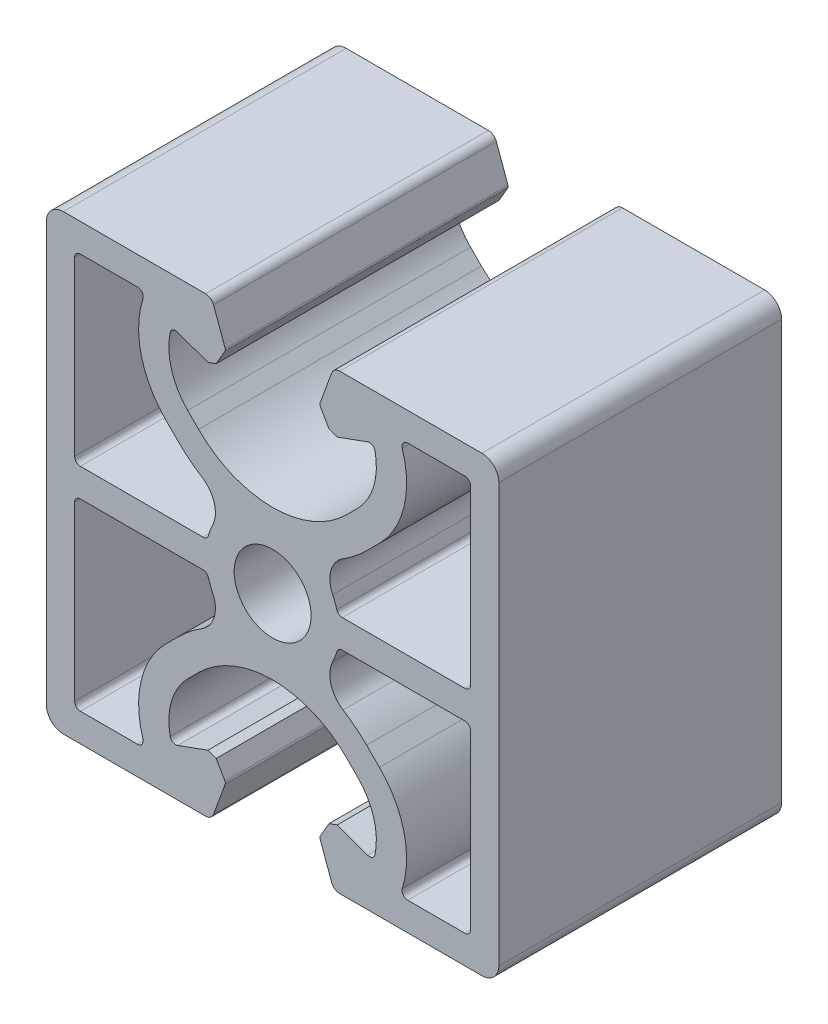
SolidWorks part; units mm, degrees
material "6005-T5"
ref_plane "Front" through (0, 0, 0) normal (0, 0, 1) x (1, 0, 0)
ref_plane "Top" through (0, 0, 0) normal (0, 1, 0) x (1, 0, 0)
ref_plane "Right" through (0, 0, 0) normal (1, 0, 0) x (0, 0, -1)
sketch "Sk Main Extrusion" plane through (0, 0, 0) normal (0, 0, 1) x (1, 0, 0)
  line L46 (-8.3085, 7.4415) -> (-9.4443, 8.5773)
  line L47 (-11.9407, 17.5) -> (-17, 17.5)
  line L48 (-17.5, 17) -> (-17.5, 1.75)
  line L49 (-17, 1.25) -> (-6.1561, 1.25)
  line L50 (-17.5, -1.75) -> (-17.5, -17)
  line L51 (-17, -17.5) -> (-11.9407, -17.5)
  line L52 (-9.4443, -8.5773) -> (-8.3085, -7.4415)
  line L53 (-6.1561, -1.25) -> (-17, -1.25)
  line L54 (9.4443, 8.5773) -> (8.3085, 7.4415)
  line L55 (6.1561, 1.25) -> (17, 1.25)
  line L56 (17.5, 1.75) -> (17.5, 17)
  line L57 (17, 17.5) -> (11.9407, 17.5)
  line L58 (-4.1901, 16.6712) -> (-5.2221, 19.5065)
  line L59 (-5.9268, 20) -> (-18.5, 20)
  line L60 (-18.5, -20) -> (-5.9268, -20)
  line L61 (-5.2221, -19.5065) -> (-4.1901, -16.6712)
  line L62 (-4.2085, -16.4607) -> (-4.9876, -15.1113)
  line L63 (-4.9876, -15.1113) -> (-5.7185, -14.8453)
  line L64 (-5.7185, -14.8453) -> (-8.3962, -15.8198)
  line L65 (-7.5042, -10.2727) -> (-6.5407, -9.3093)
  line L66 (6.5407, -9.3093) -> (7.5042, -10.2727)
  line L67 (8.3962, -15.8198) -> (5.7185, -14.8453)
  line L68 (5.7185, -14.8453) -> (4.9876, -15.1113)
  line L69 (4.9876, -15.1113) -> (4.2085, -16.4607)
  line L70 (20, -18.5) -> (20, 18.5)
  line L71 (-20, 18.5) -> (-20, -18.5)
  line L72 (8.3085, -7.4415) -> (9.4443, -8.5773)
  line L73 (11.9407, -17.5) -> (17, -17.5)
  line L74 (17.5, -17) -> (17.5, -1.75)
  line L75 (17, -1.25) -> (6.1561, -1.25)
  line L76 (4.1901, -16.6712) -> (5.2221, -19.5065)
  line L77 (5.9268, -20) -> (18.5, -20)
  line L78 (18.5, 20) -> (5.9268, 20)
  line L79 (5.2221, 19.5065) -> (4.1901, 16.6712)
  line L80 (4.2085, 16.4607) -> (4.9876, 15.1113)
  line L81 (4.9876, 15.1113) -> (5.7185, 14.8453)
  line L82 (5.7185, 14.8453) -> (8.3962, 15.8198)
  line L83 (7.5042, 10.2727) -> (6.5407, 9.3093)
  line L84 (-6.5407, 9.3093) -> (-7.5042, 10.2727)
  line L85 (-8.3962, 15.8198) -> (-5.7185, 14.8453)
  line L86 (-5.7185, 14.8453) -> (-4.9876, 15.1113)
  line L87 (-4.9876, 15.1113) -> (-4.2085, 16.4607)
  circle A55 centre (0, 0) radius 3.4
  arc A56 (-6.1561, 1.25) -> (-5.6751, 1.6133) centre (-6.1561, 1.75) ccw
  arc A57 (-5.3076, 2.5767) -> (-5.6751, 1.6133) centre (0, 0) ccw
  arc A58 (-5.3076, 2.5767) -> (-6.2308, 5.7881) centre (-7.5566, 3.6686) ccw
  arc A59 (-8.3085, 7.4415) -> (-6.2308, 5.7881) centre (0, 15.75) ccw
  arc A60 (-11.464, 16.8492) -> (-9.4443, 8.5773) centre (-3.646, 14.3755) ccw
  arc A61 (-11.464, 16.8492) -> (-11.9407, 17.5) centre (-11.9407, 17) ccw
  arc A62 (-17, 17.5) -> (-17.5, 17) centre (-17, 17) ccw
  arc A63 (-17.5, 1.75) -> (-17, 1.25) centre (-17, 1.75) ccw
  arc A64 (-5.2221, 19.5065) -> (-5.9268, 20) centre (-5.9268, 19.25) ccw
  arc A65 (-5.9268, -20) -> (-5.2221, -19.5065) centre (-5.9268, -19.25) ccw
  arc A66 (-4.1901, -16.6712) -> (-4.2085, -16.4607) centre (-4.425, -16.5857) ccw
  arc A67 (-9.057, -15.4507) -> (-8.3962, -15.8198) centre (-8.5672, -15.35) ccw
  arc A68 (-7.5042, -10.2727) -> (-9.057, -15.4507) centre (-3.4737, -14.3032) ccw
  arc A69 (6.5407, -9.3093) -> (-6.5407, -9.3093) centre (0, -15.85) ccw
  arc A70 (9.057, -15.4507) -> (7.5042, -10.2727) centre (3.4737, -14.3032) ccw
  arc A71 (8.3962, -15.8198) -> (9.057, -15.4507) centre (8.5672, -15.35) ccw
  arc A72 (4.2085, -16.4607) -> (4.1901, -16.6712) centre (4.425, -16.5857) ccw
  arc A73 (18.5, -20) -> (20, -18.5) centre (18.5, -18.5) ccw
  arc A74 (20, 18.5) -> (18.5, 20) centre (18.5, 18.5) ccw
  arc A75 (-18.5, 20) -> (-20, 18.5) centre (-18.5, 18.5) ccw
  arc A76 (-20, -18.5) -> (-18.5, -20) centre (-18.5, -18.5) ccw
  arc A77 (-17, -1.25) -> (-17.5, -1.75) centre (-17, -1.75) ccw
  arc A78 (-17.5, -17) -> (-17, -17.5) centre (-17, -17) ccw
  arc A79 (-11.9407, -17.5) -> (-11.464, -16.8492) centre (-11.9407, -17) ccw
  arc A80 (-9.4443, -8.5773) -> (-11.464, -16.8492) centre (-3.646, -14.3755) ccw
  arc A81 (-6.2308, -5.7881) -> (-8.3085, -7.4415) centre (0, -15.75) ccw
  arc A82 (-6.2308, -5.7881) -> (-5.3076, -2.5767) centre (-7.5566, -3.6686) ccw
  arc A83 (-5.6751, -1.6133) -> (-5.3076, -2.5767) centre (0, 0) ccw
  arc A84 (-5.6751, -1.6133) -> (-6.1561, -1.25) centre (-6.1561, -1.75) ccw
  arc A85 (11.9407, 17.5) -> (11.464, 16.8492) centre (11.9407, 17) ccw
  arc A86 (9.4443, 8.5773) -> (11.464, 16.8492) centre (3.646, 14.3755) ccw
  arc A87 (6.2308, 5.7881) -> (8.3085, 7.4415) centre (0, 15.75) ccw
  arc A88 (6.2308, 5.7881) -> (5.3076, 2.5767) centre (7.5566, 3.6686) ccw
  arc A89 (5.6751, 1.6133) -> (5.3076, 2.5767) centre (0, 0) ccw
  arc A90 (5.6751, 1.6133) -> (6.1561, 1.25) centre (6.1561, 1.75) ccw
  arc A91 (17, 1.25) -> (17.5, 1.75) centre (17, 1.75) ccw
  arc A92 (17.5, 17) -> (17, 17.5) centre (17, 17) ccw
  arc A93 (6.1561, -1.25) -> (5.6751, -1.6133) centre (6.1561, -1.75) ccw
  arc A94 (5.3076, -2.5767) -> (5.6751, -1.6133) centre (0, 0) ccw
  arc A95 (5.3076, -2.5767) -> (6.2308, -5.7881) centre (7.5566, -3.6686) ccw
  arc A96 (8.3085, -7.4415) -> (6.2308, -5.7881) centre (0, -15.75) ccw
  arc A97 (11.464, -16.8492) -> (9.4443, -8.5773) centre (3.646, -14.3755) ccw
  arc A98 (11.464, -16.8492) -> (11.9407, -17.5) centre (11.9407, -17) ccw
  arc A99 (17, -17.5) -> (17.5, -17) centre (17, -17) ccw
  arc A100 (17.5, -1.75) -> (17, -1.25) centre (17, -1.75) ccw
  arc A101 (5.2221, -19.5065) -> (5.9268, -20) centre (5.9268, -19.25) ccw
  arc A102 (5.9268, 20) -> (5.2221, 19.5065) centre (5.9268, 19.25) ccw
  arc A103 (4.1901, 16.6712) -> (4.2085, 16.4607) centre (4.425, 16.5857) ccw
  arc A104 (9.057, 15.4507) -> (8.3962, 15.8198) centre (8.5672, 15.35) ccw
  arc A105 (7.5042, 10.2727) -> (9.057, 15.4507) centre (3.4737, 14.3032) ccw
  arc A106 (-6.5407, 9.3093) -> (6.5407, 9.3093) centre (0, 15.85) ccw
  arc A107 (-9.057, 15.4507) -> (-7.5042, 10.2727) centre (-3.4737, 14.3032) ccw
  arc A108 (-8.3962, 15.8198) -> (-9.057, 15.4507) centre (-8.5672, 15.35) ccw
  arc A109 (-4.2085, 16.4607) -> (-4.1901, 16.6712) centre (-4.425, 16.5857) ccw
  point P29 (0, 0)
extrude "Main Extrusion" add sketch "Sk Main Extrusion" against normal blind 25
sketch "Threaded Insert Mate Sketch" plane through (0, 0, 0) normal (0, 0, 1) x (1, 0, 0)
  line L0 (-20, 0) -> (20, 0) construction
  line L3 (20, -18.5) -> (20, 18.5) construction
  line L4 (-20, 18.5) -> (-20, -18.5) construction
  circle A0 centre (0, 12.7) radius 5.6515
  circle A1 centre (0, -12.7) radius 5.6515
  dimension "D2" = 11.303
  dimension "D1" = 12.7
equation "\"Weight kg\"= round ( \"SW-Mass\" , 2 )"
equation "\"Weight lbs\"= round ( \"SW-Mass\" * 2.2046 , 2 )"
equation "\"Length mm\"= round ( \"Length@Main Extrusion\" , 2 )"
equation "\"Length in\"= round ( \"Length@Main Extrusion\" / 25.4 , 3 )"
